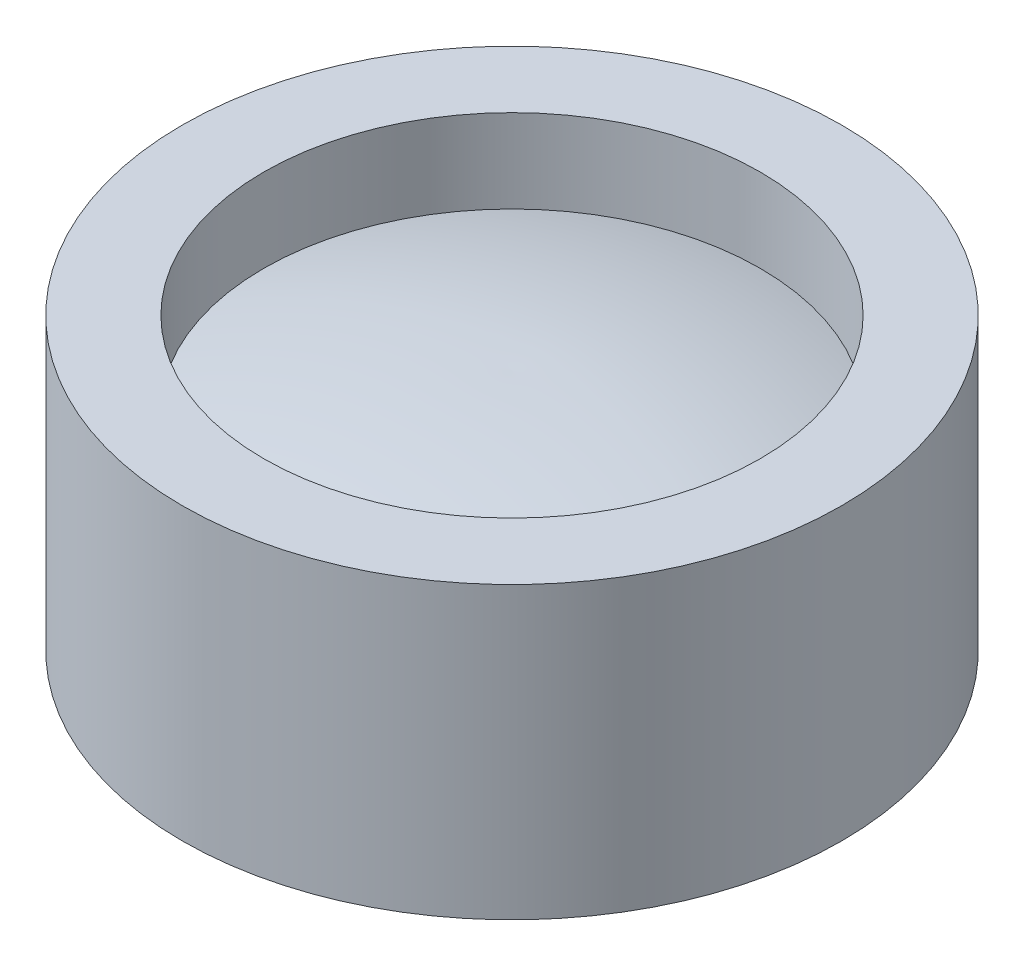
SolidWorks part; units mm, degrees
ref_plane "Front Plane" through (0, 0, 0) normal (0, 0, 1) x (1, 0, 0)
ref_plane "Top Plane" through (0, 0, 0) normal (0, 1, 0) x (1, 0, 0)
ref_plane "Right Plane" through (0, 0, 0) normal (1, 0, 0) x (0, 0, -1)
sketch "Sketch1" plane through (0, 0, 0) normal (0, 0, 1) x (1, 0, 0)
  line L0 (0, 0) -> (1.88, 0)
  line L1 (1.88, 0) -> (1.88, -0.2)
  line L2 (1.88, -0.2) -> (2.43, -0.2)
  line L3 (2.43, -0.2) -> (2.43, 1.94)
  line L4 (2.43, 1.94) -> (1.83, 1.94)
  line L5 (1.83, 1.94) -> (1.83, 1.325)
  line L6 (0, 0) -> (0, 1.59)
  spline S0 degree 2 poles (1.83, 1.325) (0.9313, 1.6064) (0, 1.59) knots 0 0 0 1 1 1
  dimension "D1" = 0.55
  dimension "D2" = 2.14
  dimension "D3" = 2.43
  dimension "D4" = 0.2
  dimension "D5" = 0.35
  dimension "D6" = 0.6
  dimension "D7" = 0.25
  dimension "D8" = 1.3
revolve "Revolve1" add sketch "Sketch1" angle 360 about L6
